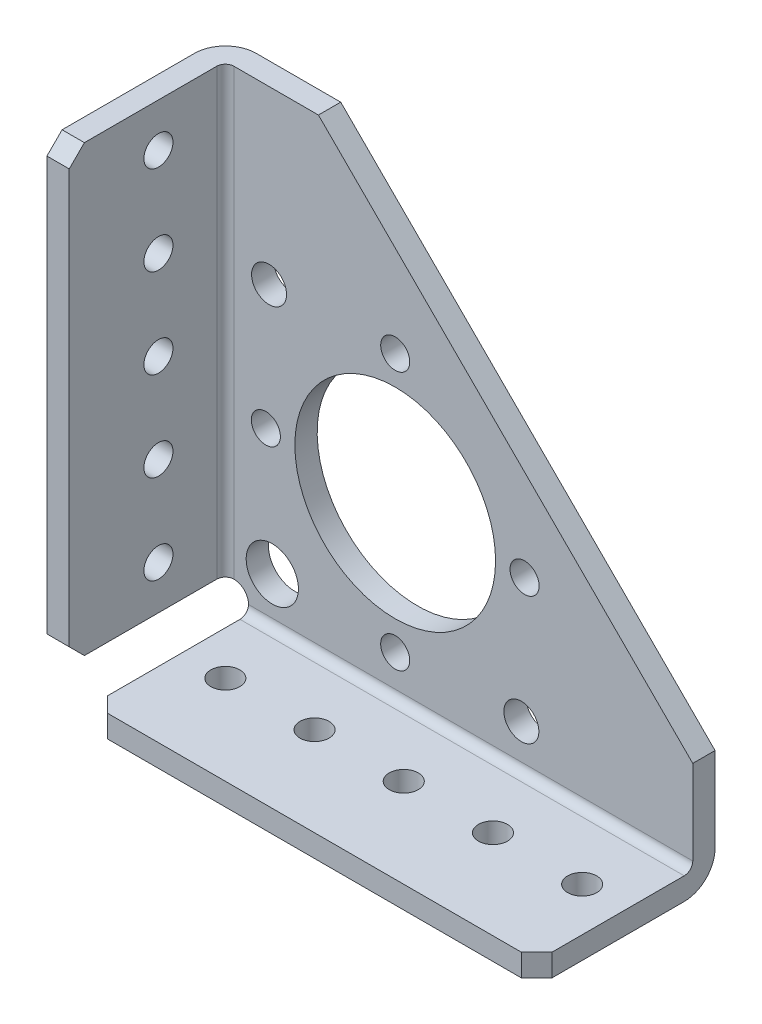
SolidWorks part; units mm, degrees
ref_plane "Front Plane" through (0, 0, 0) normal (0, 0, 1) x (1, 0, 0)
ref_plane "Top Plane" through (0, 0, 0) normal (0, 1, 0) x (1, 0, 0)
ref_plane "Right Plane" through (0, 0, 0) normal (1, 0, 0) x (0, 0, -1)
ref_plane "Plane1" through (0, 0, 0) normal (0, 0, -1) x (-1, 0, 0)
sketch "Sketch1" plane through (0, 0, 0) normal (0, 0, -1) x (-1, 0, 0)
  line L0 (-69.723, 0) -> (0, 0)
  line L1 (0, 0) -> (0, 69.723)
  line L2 (0, 69.723) -> (-16.4281, 69.723)
  line L3 (-16.4281, 69.723) -> (-69.723, 16.4281)
  line L4 (-69.723, 16.4281) -> (-69.723, 0)
extrude "Boss-Extrude1" add sketch "Sketch1" against normal blind 3.175
sketch "Sketch2" plane through (0, 0, 0) normal (0, 0, -1) x (-1, 0, 0)
  line L0 (-6.477, 6.477) -> (-6.477, 0)
  line L1 (-6.477, 0) -> (0, 0)
  line L2 (0, 0) -> (0, 6.477)
  line L3 (0, 6.477) -> (-6.477, 6.477)
extrude "Cut-Extrude1" cut sketch "Sketch2" against normal through all
sketch "Sketch3" plane through (0, 0, 3.175) normal (0, 0, 1) x (1, 0, 0)
  line L0 (6.477, 3.175) -> (69.723, 3.175)
  line L1 (69.723, 3.175) -> (69.723, 0)
  line L2 (69.723, 0) -> (6.477, 0)
  line L3 (6.477, 0) -> (6.477, 3.175)
extrude "Boss-Extrude2" add sketch "Sketch3" along normal blind 22.225
sketch "Sketch4" plane through (0, 0, 3.175) normal (0, 0, 1) x (1, 0, 0)
  line L0 (3.175, 69.723) -> (3.175, 6.477)
  line L1 (3.175, 6.477) -> (0, 6.477)
  line L2 (0, 6.477) -> (0, 69.723)
  line L3 (0, 69.723) -> (3.175, 69.723)
extrude "Boss-Extrude3" add sketch "Sketch4" along normal blind 22.225
hole_wizard "M6.5 Clearance Hole1" positions "Sketch6" profile "Sketch5" hole size "M6.5" standard "ANSI Metric"
sketch "Sketch6" plane through (0, 0, 0) normal (0, 0, -1) x (-1, 0, 0)
  point P0 (-9.8594, 9.8594)
sketch "Sketch5" plane through (9.8594, 9.8594, 0) normal (1, 0, 0) x (0, 1, 0)
  line L0 (0, 0) -> (0, 25.4)
  line L1 (0, 25.4) -> (3.7211, 25.4)
  line L2 (3.7211, 25.4) -> (3.7211, 0)
  line L5 (3.7211, 0) -> (0, 0)
  line L11 (0, -6.35) -> (0, 107.95) construction
  dimension "Thru Hole Dia." = 7.4422
  dimension "Thru Hole Depth" = 25.4
hole_wizard "M25 Clearance Hole1" positions "Sketch8" profile "Sketch7" hole size "M25" standard "ANSI Metric"
sketch "Sketch8" plane through (0, 0, 0) normal (0, 0, -1) x (-1, 0, 0)
  point P0 (-27.3601, 27.3601)
sketch "Sketch7" plane through (27.3601, 27.3601, 0) normal (1, 0, 0) x (0, 1, 0)
  line L0 (0, 0) -> (0, 25.4)
  line L1 (0, 25.4) -> (14.2875, 25.4)
  line L2 (14.2875, 25.4) -> (14.2875, 0)
  line L5 (14.2875, 0) -> (0, 0)
  line L11 (0, -6.35) -> (0, 107.95) construction
  dimension "Thru Hole Dia." = 28.575
  dimension "Thru Hole Depth" = 25.4
hole_wizard "Hole1" positions "Sketch10" profile "Sketch9" legacy
sketch "Sketch10" plane through (0, 0, 0) normal (0, 0, -1) x (-1, 0, 0)
  point P0 (-9.3996, 45.3206)
  point P1 (-45.3206, 9.3996)
sketch "Sketch9" plane through (9.3996, 45.3206, 0) normal (1, 0, 0) x (0, 1, 0)
  line L0 (0, 0) -> (0, 25.4)
  line L1 (0, 25.4) -> (2.4892, 25.4)
  line L2 (2.4892, 25.4) -> (2.4892, 0)
  line L3 (2.4892, 0) -> (0, 0)
  line L4 (0, 110) -> (0, -10) construction
  dimension "Diameter" = 4.9784
  dimension "Depth" = 25.4
hole_wizard "M3.5 Clearance Hole1" positions "Sketch12" profile "Sketch11" hole size "M3.5" standard "ANSI Metric"
sketch "Sketch12" plane through (0, 0, 0) normal (0, 0, -1) x (-1, 0, 0)
  point P0 (-45.7751, 27.3601)
  point P1 (-8.9451, 27.3601)
  point P2 (-27.3601, 45.7751)
  point P3 (-27.3601, 8.9451)
sketch "Sketch11" plane through (45.7751, 27.3601, 0) normal (1, 0, 0) x (0, 1, 0)
  line L0 (0, 0) -> (0, 25.4)
  line L1 (0, 25.4) -> (2.0701, 25.4)
  line L2 (2.0701, 25.4) -> (2.0701, 0)
  line L5 (2.0701, 0) -> (0, 0)
  line L11 (0, -6.35) -> (0, 107.95) construction
  dimension "Thru Hole Dia." = 4.1402
  dimension "Thru Hole Depth" = 25.4
hole_wizard "M3.5 Clearance Hole2" positions "Sketch14" profile "Sketch13" hole size "M3.5" standard "ANSI Metric"
sketch "Sketch14" plane through (3.175, 0, 0) normal (1, 0, 0) x (0, 0, -1)
  point P0 (-12.7, 63.5)
  point P1 (-12.7, 50.8)
  point P2 (-12.7, 38.1)
  point P3 (-12.7, 25.4)
  point P4 (-12.7, 12.7)
sketch "Sketch13" plane through (3.175, 63.5, 12.7) normal (0, 1, 0) x (0, 0, -1)
  line L0 (0, 0) -> (0, 3.175)
  line L1 (0, 3.175) -> (2.0701, 3.175)
  line L2 (2.0701, 3.175) -> (2.0701, 0)
  line L5 (2.0701, 0) -> (0, 0)
  line L11 (0, -6.35) -> (0, 107.95) construction
  dimension "Thru Hole Dia." = 4.1402
  dimension "Thru Hole Depth" = 3.175
hole_wizard "M3.5 Clearance Hole3" positions "Sketch16" profile "Sketch15" hole size "M3.5" standard "ANSI Metric"
sketch "Sketch16" plane through (0, 3.175, 0) normal (0, 1, 0) x (1, 0, 0)
  point P0 (63.5, -12.7)
  point P1 (50.8, -12.7)
  point P2 (38.1, -12.7)
  point P3 (25.4, -12.7)
  point P4 (12.7, -12.7)
sketch "Sketch15" plane through (63.5, 3.175, 12.7) normal (1, 0, 0) x (0, 0, 1)
  line L0 (0, 0) -> (0, 3.175)
  line L1 (0, 3.175) -> (2.0701, 3.175)
  line L2 (2.0701, 3.175) -> (2.0701, 0)
  line L5 (2.0701, 0) -> (0, 0)
  line L11 (0, -6.35) -> (0, 107.95) construction
  dimension "Thru Hole Dia." = 4.1402
  dimension "Thru Hole Depth" = 3.175
chamfer "Chamfer1" distance 2.159 angle 45 4 edges at (1.5875, 6.477, 25.4) (1.5875, 69.723, 25.4) (6.477, 1.5875, 25.4) (69.723, 1.5875, 25.4)
fillet "Fillet1" radius 1.2192 2 edges at (3.175, 38.1, 3.175)
fillet "Fillet2" radius 2.0701 1 edges at (6.477, 6.477, 1.5875)
fillet "Fillet3" radius 4.3942 2 edges at (38.1, 0, 0) (0, 38.1, 0)
